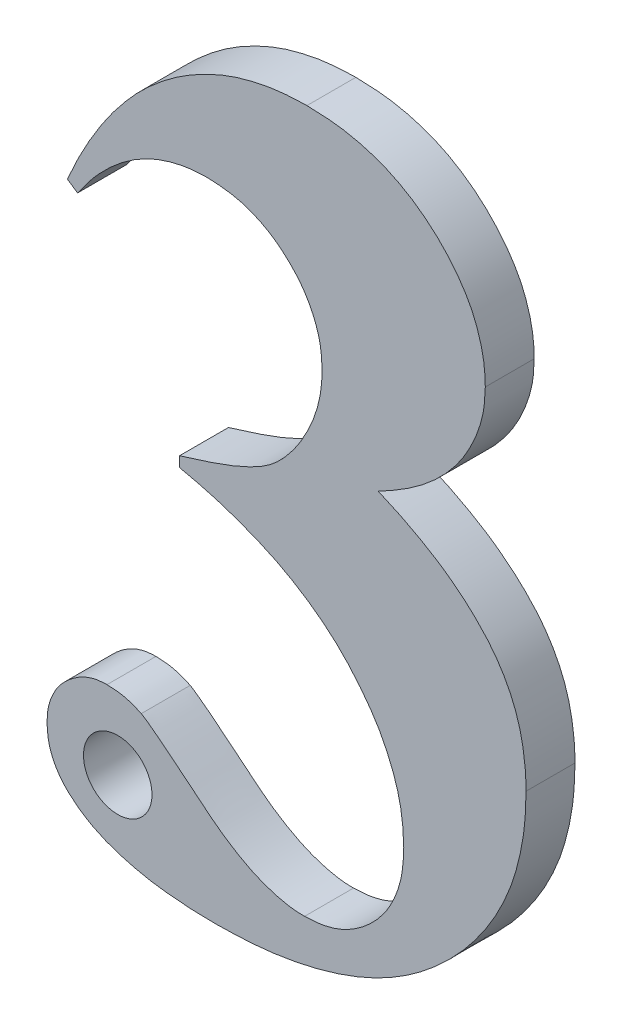
SolidWorks part; units mm, degrees
ref_plane "Plan de face" through (0, 0, 0) normal (0, 0, 1) x (1, 0, 0)
ref_plane "Plan de dessus" through (0, 0, 0) normal (0, 1, 0) x (1, 0, 0)
ref_plane "Plan de droite" through (0, 0, 0) normal (1, 0, 0) x (0, 0, -1)
sketch "Esquisse1" plane through (0, 0, 0) normal (0, 0, 1) x (1, 0, 0)
  text T0 "<b>3</b>\r\n" font "Times New Roman" height 30
extrude "Boss.-Extru.1" add sketch "Esquisse1" along normal blind 2
hole_wizard "Dégagement M1.61" positions "Esquisse2" profile "Esquisse3" hole size "M1.6" standard "Ansi Metric"
sketch "Esquisse2" plane through (0, 0, 2) normal (0, 0, 1) x (1, 0, 0)
  point P8 (15.4338, 14.0595)
  point P13 (15.4338, 14.0595)
  point P16 (16.0915, 13.808)
  point P17 (15.4338, 14.0595)
sketch "Esquisse3" plane through (15.4338, 14.0595, 2) normal (1, 0, 0) x (0, -1, 0)
  line L0 (0, 0) -> (0, 50)
  line L1 (0, 50) -> (1.4, 50)
  line L2 (1.4, 50) -> (1.4, 0)
  line L5 (1.4, 0) -> (0, 0)
  line L10 (0, 50) -> (-1.4, 50) construction
  line L11 (0, -6.35) -> (0, 107.95) construction
  dimension "Diamètre du perçage" = 2.8
  dimension "Profondeur du perçage" = 50
  dimension "Angle de pointe" = 180
